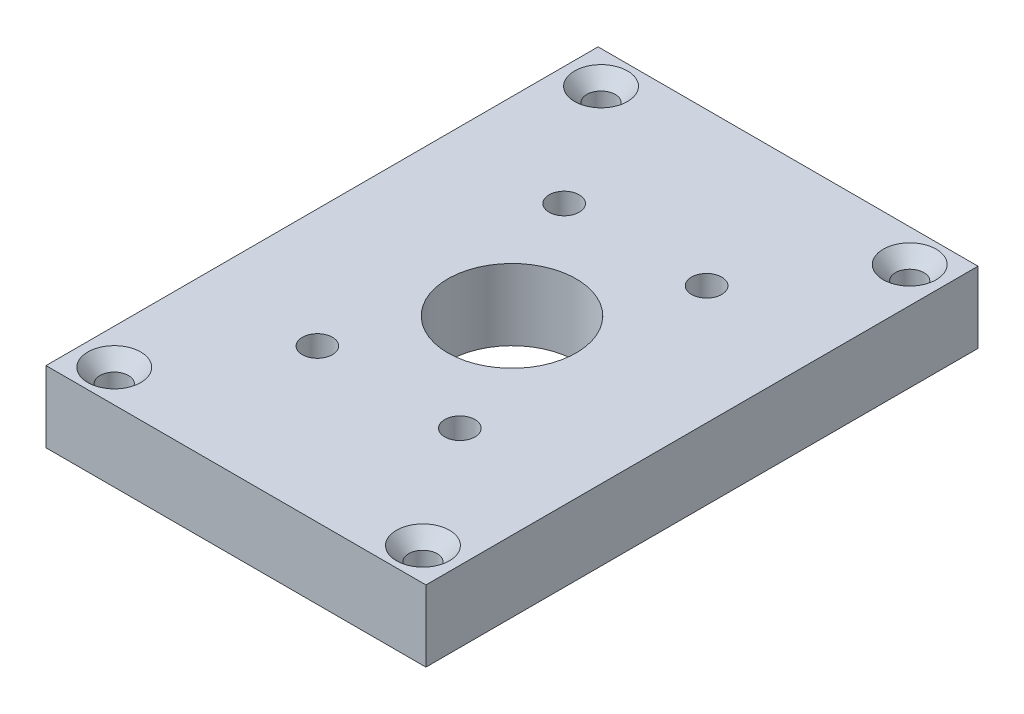
SolidWorks part; units mm, degrees
ref_plane "Front Plane" through (0, 0, 0) normal (0, 0, 1) x (1, 0, 0)
ref_plane "Top Plane" through (0, 0, 0) normal (0, 1, 0) x (1, 0, 0)
ref_plane "Right Plane" through (0, 0, 0) normal (1, 0, 0) x (0, 0, -1)
sketch "Sketch1" plane through (0, 0, 0) normal (0, 1, 0) x (1, 0, 0)
  line L0 (-25.4, -37.3063) -> (25.4, -37.3063) construction
  line L1 (-25.4, -36.9094) -> (25.4, -36.9094)
  line L2 (-25.4, -36.9094) -> (-25.4, 36.9094)
  line L3 (-25.4, 36.9094) -> (25.4, 36.9094)
  line L4 (25.4, -36.9094) -> (25.4, 36.9094)
  line L5 (-25.4, -36.9094) -> (25.4, 36.9094) construction
  line L6 (-25.4, 36.9094) -> (25.4, -36.9094) construction
  point P0 (0, 0)
  dimension "D1" = 0.3969
extrude "Boss-Extrude1" add sketch "Sketch1" along normal blind 9.525
hole_wizard "CSK for #6 Flat Head Machine Screw1" positions "Sketch3" profile "Sketch2" countersink size "#6" standard "Ansi Inch" end condition through all
sketch "Sketch3" plane through (0, 9.525, 0) normal (0, 1, 0) x (-1, 0, 0)
  point P1 (20.6375, -32.5437)
  point P4 (-20.6375, -32.5437)
  point P7 (-20.6375, 32.5438)
  point P10 (20.6375, 32.5438)
sketch "Sketch2" plane through (-20.6375, 9.525, -32.5437) normal (1, 0, 0) x (0, 0, 1)
  line L0 (0, 0) -> (0, 9.525)
  line L1 (0, 9.525) -> (1.8986, 9.525)
  line L2 (1.8986, 9.525) -> (1.8986, 1.892)
  line L3 (1.8986, 1.892) -> (3.5433, 0)
  line L5 (3.5433, 0) -> (0, 0)
  line L6 (-1.8986, 1.892) -> (-3.5433, 0) construction
  line L11 (0, -6.35) -> (0, 107.95) construction
  dimension "Thru Hole Dia." = 3.7973
  dimension "Thru Hole Depth" = 9.525
  dimension "Near C'Sink Dia." = 7.0866
  dimension "Near C'Sink Angle" = 82
sketch "Sketch4" plane through (0, 0, 0) normal (0, -1, 0) x (-1, 0, 0)
  line L0 (-11.1125, 34.6075) -> (11.1125, 34.6075)
  line L1 (-11.1125, -32.4231) -> (11.1125, -32.4231)
  line L2 (-17.4625, -26.0731) -> (-17.4625, 26.0731)
  line L3 (-11.1125, 32.4231) -> (11.1125, 32.4231)
  line L4 (17.4625, -26.0731) -> (17.4625, 26.0731)
  line L5 (-17.4625, -32.4231) -> (17.4625, 32.4231) construction
  line L6 (-17.4625, 32.4231) -> (17.4625, -32.4231) construction
  line L7 (19.6469, -26.0731) -> (19.6469, 26.0731)
  line L8 (-11.1125, -34.6075) -> (11.1125, -34.6075)
  line L9 (-19.6469, -26.0731) -> (-19.6469, 26.0731)
  arc A0 (-11.1125, -32.4231) -> (-17.4625, -26.0731) centre (-11.1125, -26.0731) cw
  arc A1 (11.1125, -32.4231) -> (17.4625, -26.0731) centre (11.1125, -26.0731) ccw
  arc A2 (11.1125, 32.4231) -> (17.4625, 26.0731) centre (11.1125, 26.0731) cw
  arc A3 (-17.4625, 26.0731) -> (-11.1125, 32.4231) centre (-11.1125, 26.0731) cw
  arc A4 (11.1125, 34.6075) -> (19.6469, 26.0731) centre (11.1125, 26.0731) cw
  arc A5 (11.1125, -34.6075) -> (19.6469, -26.0731) centre (11.1125, -26.0731) ccw
  arc A6 (-11.1125, -34.6075) -> (-19.6469, -26.0731) centre (-11.1125, -26.0731) cw
  arc A7 (-19.6469, 26.0731) -> (-11.1125, 34.6075) centre (-11.1125, 26.0731) cw
  point P0 (0, 0)
  dimension "D1" = 6.35
  dimension "D2" = 2.1844
  dimension "D3" = 22.225
  dimension "D4" = 52.1462
extrude "Cut-Extrude1 - dash 036" cut sketch "Sketch4" against normal blind 1.3208
sketch "Sketch5" plane through (0, 9.525, 0) normal (0, 1, 0) x (1, 0, 0)
  line L0 (25.4, 36.9094) -> (-25.4, 36.9094) construction
  circle A4 centre (0, 0) radius 8.5852
  point P3 (0, 36.9094)
extrude "Cut-Extrude1" cut sketch "Sketch5" against normal through all
sketch "Sketch8" plane through (0, 9.525, 0) normal (0, 1, 0) x (-1, 0, 0)
  line L0 (31.6062, 0) -> (-30.5429, 0) construction
  line L1 (0, 0) -> (-8.0091, -13.8721) construction
  circle A0 centre (0, 0) radius 19.05 construction
  point P5 (-9.525, -16.4978)
  dimension "D1" = 38.1
  dimension "D2" = 60
hole_wizard "#10-32 Tapped Hole2" positions "Sketch10" profile "Sketch9" tap size "#10-32" standard "Ansi Inch"
sketch "Sketch10" plane through (0, 9.525, 0) normal (0, 1, 0) x (-1, 0, 0)
  point P1 (-9.525, -16.4978)
sketch "Sketch9" plane through (9.525, 9.525, -16.4978) normal (1, 0, 0) x (0, 0, 1)
  line L0 (0, 0) -> (0, 7.5633)
  line L1 (0, 7.5633) -> (2.0193, 6.35)
  line L2 (2.0193, 6.35) -> (2.0193, 0)
  line L5 (2.0193, 0) -> (0, 0)
  line L10 (0, 7.5633) -> (-2.0193, 6.35) construction
  line L11 (0, -6.35) -> (0, 107.95) construction
  dimension "Tap Drill Dia." = 4.0386
  dimension "Tap Drill Depth" = 6.35
  dimension "Drill Angle" = 118
pattern_circular "CirPattern1" count 6 over 360 about axis through (0, 0, 0) along (0, 1, 0) skipping 2, 5 of "#10-32 Tapped Hole2"
